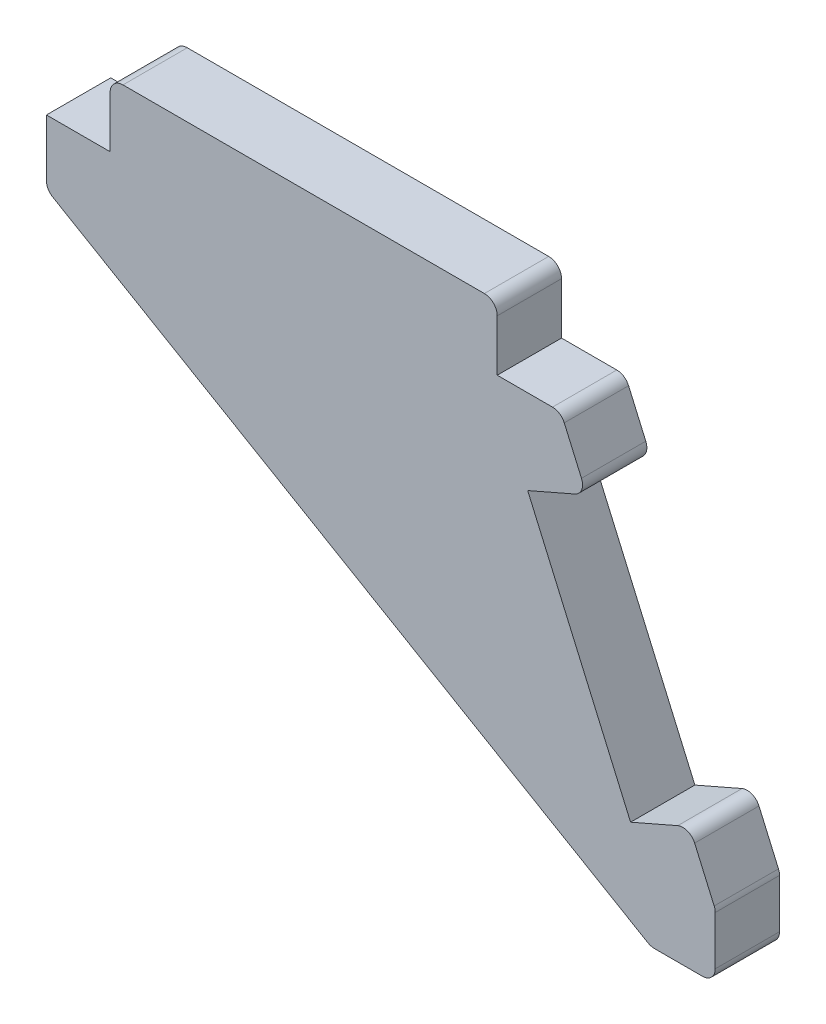
SolidWorks part; units mm, degrees
ref_plane "Front" through (0, 0, 0) normal (0, 0, 1) x (1, 0, 0)
ref_plane "Top" through (0, 0, 0) normal (0, 1, 0) x (1, 0, 0)
ref_plane "Right" through (0, 0, 0) normal (1, 0, 0) x (0, 0, -1)
sketch "Sketch1" plane through (0, 0, 0) normal (0, 0, 1) x (1, 0, 0)
  line L0 (4.95, 5) -> (40, 5) construction
  line L1 (4.95, 5) -> (4.95, 0) construction
  line L2 (35.05, 0) -> (40, 0) construction
  line L3 (40, 5) -> (40, 0) construction
  line L4 (40, 0) -> (42, -4.5826) construction
  line L5 (52, -27.4955) -> (47.4174, -29.4955) construction
  line L6 (47.4174, -29.4955) -> (35.4174, -2) construction
  line L7 (35.4174, -2) -> (40, 0) construction
  line L8 (42, -4.5826) -> (37.4174, -6.5826)
  line L9 (37.4174, -6.5826) -> (45.4174, -24.9129)
  line L10 (45.4174, -24.9129) -> (50, -22.9129)
  line L12 (35.05, 5) -> (4.95, 5)
  line L13 (35.05, 5) -> (35.05, 0)
  line L15 (4.95, 5) -> (4.95, 0)
  line L16 (50, -22.9129) -> (52, -27.4955) construction
  line L17 (50, -22.9129) -> (52, -27.4955)
  line L18 (52, -27.4955) -> (52, -32.4955)
  line L19 (42, -4.5826) -> (40, 0)
  line L20 (40, 0) -> (35.05, 0)
  line L21 (4.95, 0) -> (0, 0)
  line L22 (0, 0) -> (0, -5)
  line L23 (0, -5) -> (47, -32.4955)
  line L24 (47, -32.4955) -> (52, -32.4955)
  dimension "D1" = 30
  dimension "D2" = 20
  dimension "D3" = 4.95
  dimension "D4" = 5
  dimension "D5" = 5
  dimension "D6" = 5
  dimension "D7" = 4.95
extrude "Boss-Extrude1" add sketch "Sketch1" along normal blind 5
fillet "Fillet1" radius 1 9 edges at (40, 0, 2.5) (0, -5, 2.5) (52, -27.4955, 2.5) (52, -32.4955, 2.5) (47, -32.4955, 2.5) (50, -22.9129, 2.5) (42, -4.5826, 2.5) (35.05, 5, 2.5) (4.95, 5, 2.5)
